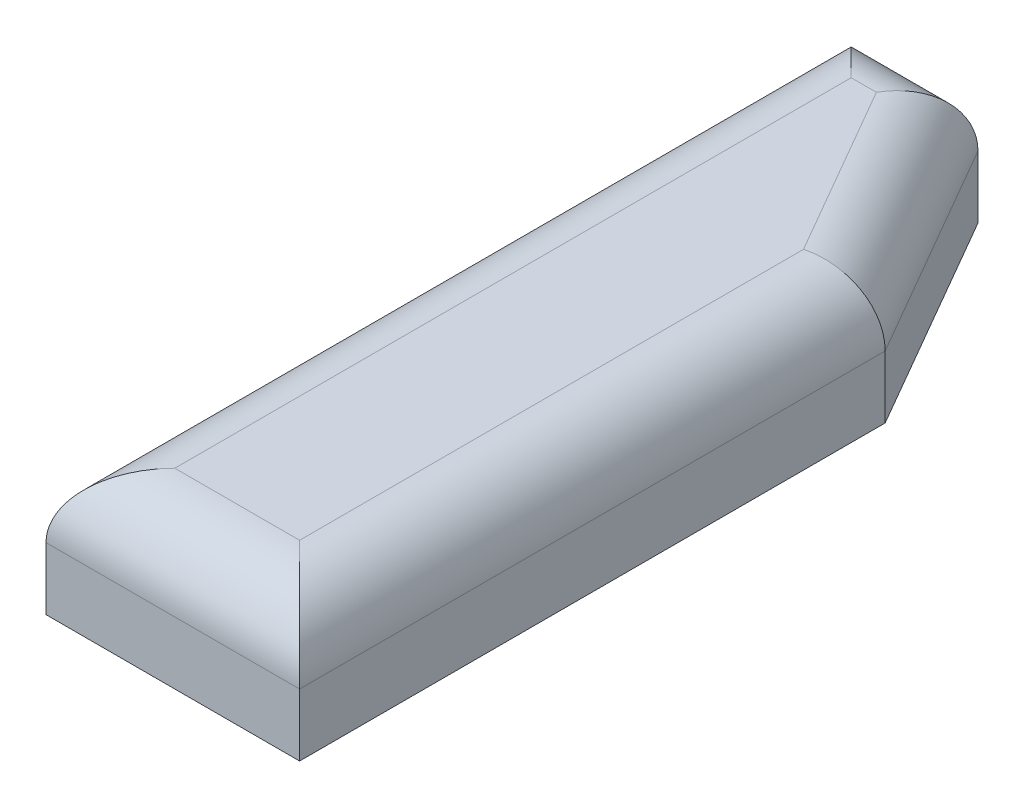
SolidWorks part; units mm, degrees
ref_plane "Front Plane" through (0, 0, 0) normal (0, 0, 1) x (1, 0, 0)
ref_plane "Top Plane" through (0, 0, 0) normal (0, 1, 0) x (1, 0, 0)
ref_plane "Right Plane" through (0, 0, 0) normal (1, 0, 0) x (0, 0, -1)
sketch "Sketch1" plane through (0, 0, 0) normal (0, 1, 0) x (1, 0, 0)
  line L0 (10, -31.75) -> (10, 14.4295)
  line L1 (10, 14.4295) -> (0, 31.75)
  line L2 (-10, 31.75) -> (-10, -31.75)
  line L3 (-10, -31.75) -> (10, -31.75)
  line L4 (0, 31.75) -> (-10, 31.75)
  point P2 (0, -31.75)
  point P3 (0, 4.406)
  point P5 (10, 4.8053)
  point P9 (0, 0)
  point P10 (0, 14.2888)
  point P11 (0, 28.9672)
  point P12 (-10, 0)
  dimension "D1" = 120
  dimension "D2" = 63.5
  dimension "D3" = 20
extrude "Boss-Extrude1" add sketch "Sketch1" along normal blind 10
fillet "Fillet1" radius 5.08 5 edges at (5, 10, -23.0897) (-5, 10, -31.75) (-10, 10, 0) (0, 10, 31.75) (10, 10, 8.6603)
